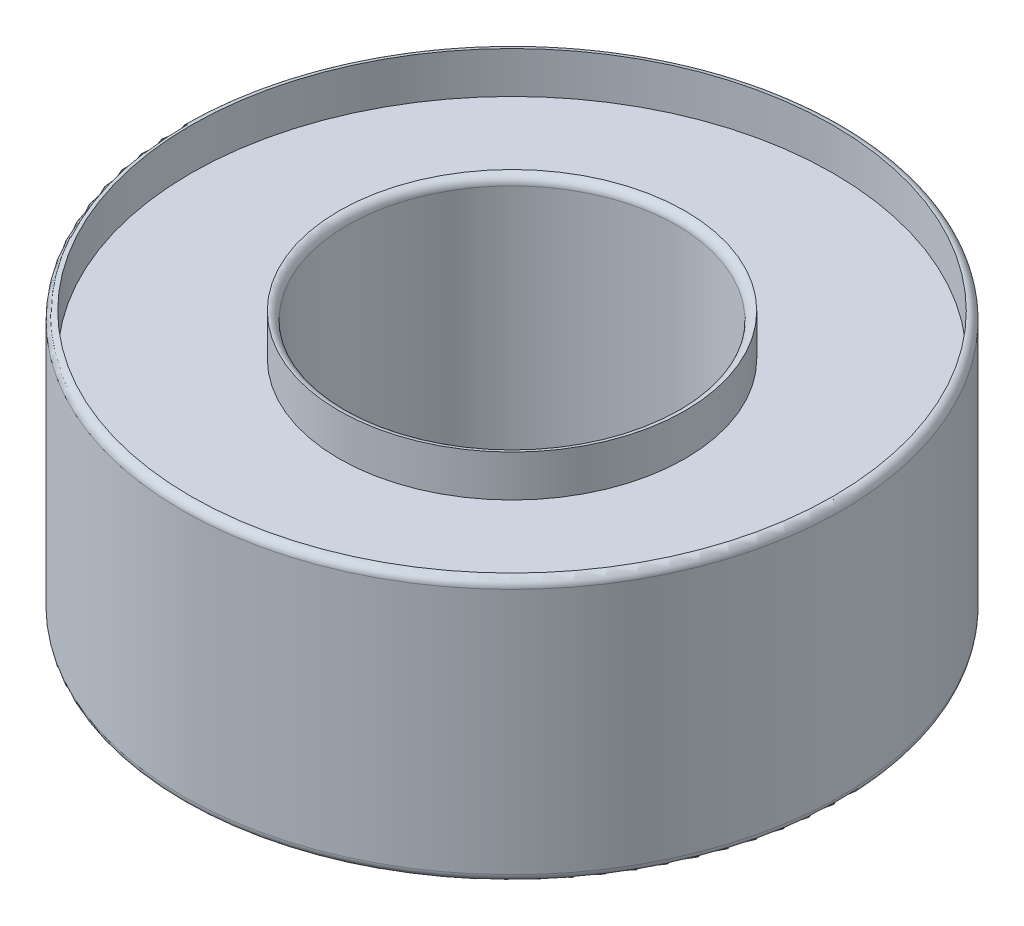
SolidWorks part; units mm, degrees
ref_plane "Front" through (0, 0, 0) normal (0, 0, 1) x (1, 0, 0)
ref_plane "Top" through (0, 0, 0) normal (0, 1, 0) x (1, 0, 0)
ref_plane "Right" through (0, 0, 0) normal (1, 0, 0) x (0, 0, -1)
sketch "Sketch1" plane through (0, 0, 0) normal (0, 1, 0) x (1, 0, 0)
  circle A0 centre (0, 0) radius 1.9844
  circle A1 centre (0, 0) radius 3.9688
  dimension "D1" = 3.9688
  dimension "D2" = 7.9375
extrude "Boss-Extrude1" add sketch "Sketch1" along normal blind 3.175
fillet "Fillet1" radius 0.1 4 edges at (0, 0, 1.9844) (0, 3.175, 1.9844) (0, 0, 3.9688) (0, 3.175, 3.9688)
sketch "Sketch2" plane through (0, 3.175, 0) normal (0, 1, 0) x (1, 0, 0)
  circle A0 centre (0, 0) radius 3.8688
  circle A1 centre (0, 0) radius 2.0844
  circle A2 centre (0, 0) radius 3.8688 construction
  circle A3 centre (0, 0) radius 2.0844 construction
extrude "Cut-Extrude1" cut sketch "Sketch2" against normal blind 0.5
sketch "Sketch3" plane through (0, 0, 0) normal (0, -1, 0) x (1, 0, 0)
  circle A0 centre (0, 0) radius 3.8688 construction
  circle A1 centre (0, 0) radius 3.8688
  circle A2 centre (0, 0) radius 2.0844 construction
  circle A3 centre (0, 0) radius 2.0844
extrude "Cut-Extrude2" cut sketch "Sketch3" against normal blind 0.5
